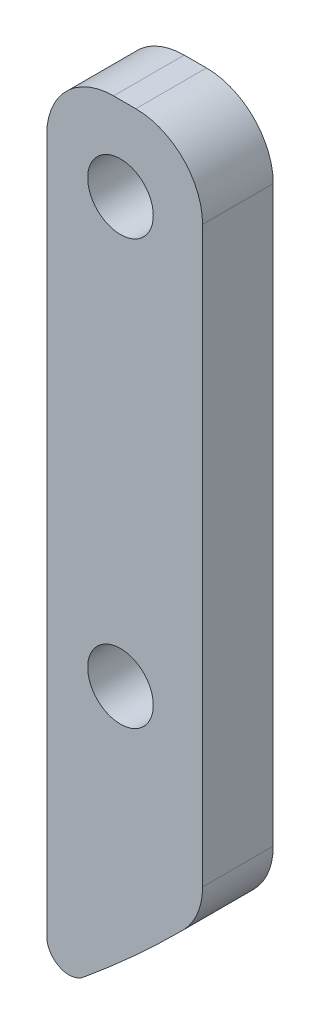
SolidWorks part; units mm, degrees
ref_plane "Front Plane" through (0, 0, 0) normal (0, 0, 1) x (1, 0, 0)
ref_plane "Top Plane" through (0, 0, 0) normal (0, 1, 0) x (1, 0, 0)
ref_plane "Right Plane" through (0, 0, 0) normal (1, 0, 0) x (0, 0, -1)
sketch "Sketch1" plane through (0, 0, 0) normal (0, 0, 1) x (1, 0, 0)
  line L1 (37.5, -12.5875) -> (37.5, -48.864)
  line L3 (44.5, -41.3657) -> (44.5, -15.5875)
  line L4 (44.5, -15.5875) -> (44.5, -12.5875)
  line L5 (44.5, -12.5875) -> (37.5, -12.5875)
  line L6 (44.5, -41.3657) -> (44.5, -42.5875)
  arc A1 (37.5, -48.864) -> (44.5, -42.5875) centre (0, 0) ccw
  circle A4 centre (40.8119, -16.3543) radius 1.4732
  circle A5 centre (40.8119, -35.4043) radius 1.4732
extrude "Boss-Extrude1" add sketch "Sketch1" along normal blind 3.175
fillet "Fillet1" radius 3 3 edges at (37.5, -12.5875, 1.5875) (44.5, -12.5875, 1.5875) (44.5, -42.5875, 1.5875)
fillet "Fillet2" radius 1 1 edges at (37.5, -48.864, 1.5875)
